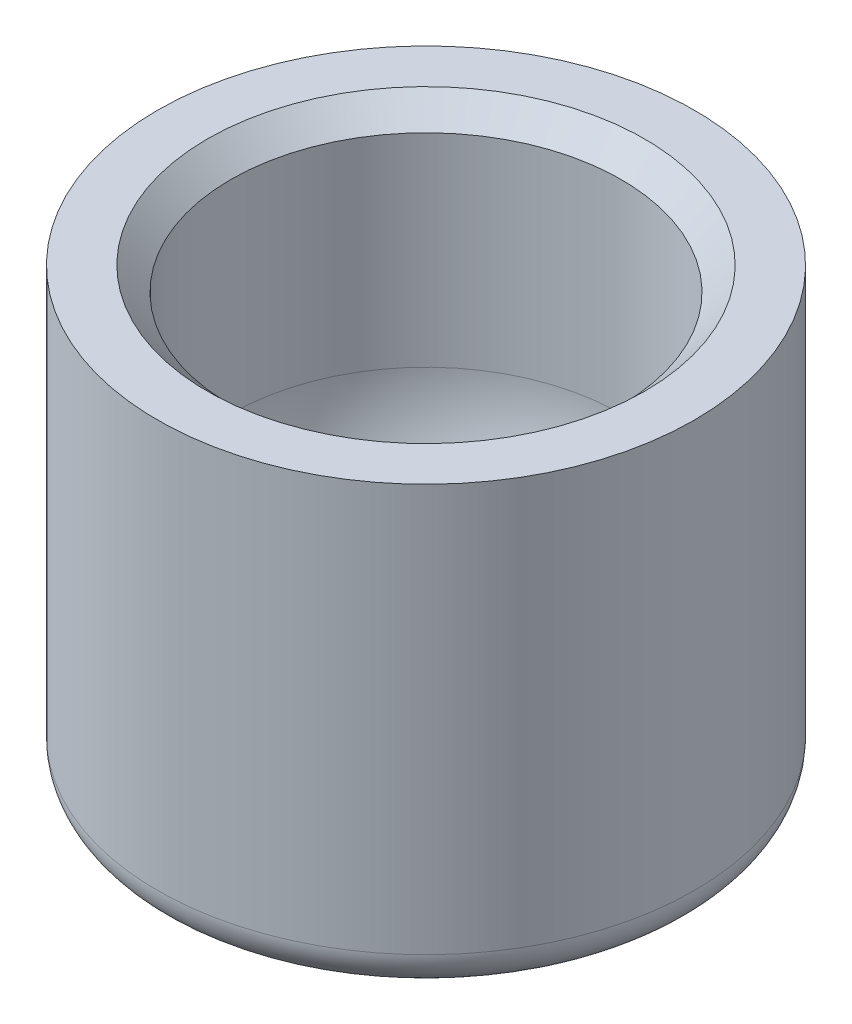
SolidWorks part; units mm, degrees
material "POLYURETHANE (11671)"
ref_plane "Front" through (0, 0, 0) normal (0, 0, 1) x (1, 0, 0)
ref_plane "Top" through (0, 0, 0) normal (0, 1, 0) x (1, 0, 0)
ref_plane "Right" through (0, 0, 0) normal (1, 0, 0) x (0, 0, -1)
sketch "Sketch1" plane through (0, 0, 0) normal (0, 0, 1) x (1, 0, 0)
  line L0 (6.35, 0) -> (8.7312, 0)
  line L1 (8.7312, 0) -> (8.7312, -13.2544)
  line L2 (8.1191, -14.3407) -> (0.635, -18.8727)
  line L3 (0, -19.05) -> (-2.54, -19.05) construction
  line L4 (6.35, 0) -> (6.35, -7.366)
  line L5 (0, -13.716) -> (0, -19.05)
  arc A0 (6.35, -7.366) -> (0, -13.716) centre (0, -7.366) cw
  arc A1 (0.635, -18.8727) -> (0, -19.05) centre (0, -17.8241) cw
  arc A2 (8.7312, -13.2544) -> (8.1191, -14.3407) centre (7.4612, -13.2544) cw
  point P13 (8.7313, -13.97)
  dimension "D3" = 2.54
  dimension "D8" = 1.27
  dimension "D1" = 6.35
  dimension "D2" = 8.7312
  dimension "D4" = 19.05
  dimension "D5" = 13.97
  dimension "D6" = 0.635
  dimension "D7" = 13.716
revolve "Revolve1" add sketch "Sketch1" angle 360 about L5
chamfer "Chamfer1" distance 0.762 angle 45 1 edges at (-6.35, 0, 0)
